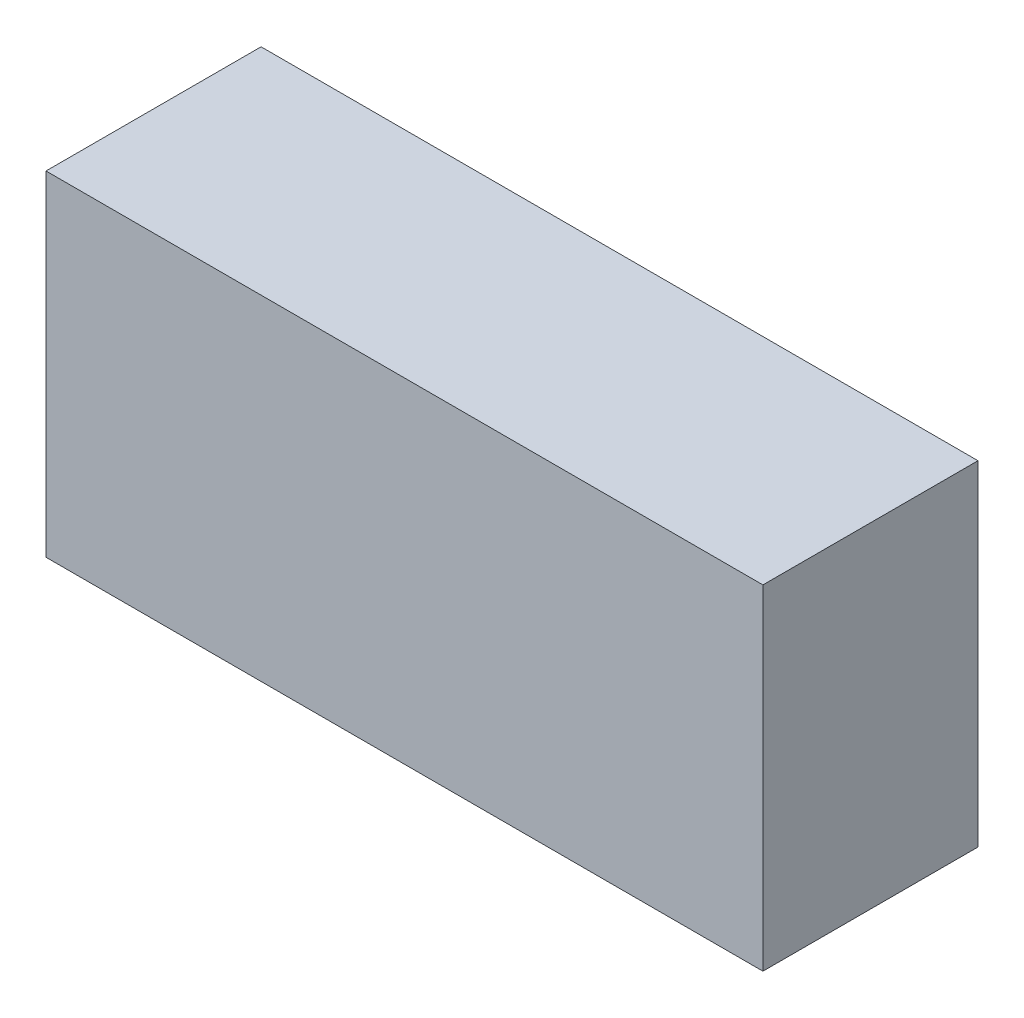
SolidWorks part; units mm, degrees
ref_plane "Спереди" through (0, 0, 0) normal (0, 0, 1) x (1, 0, 0)
ref_plane "Сверху" through (0, 0, 0) normal (0, 1, 0) x (1, 0, 0)
ref_plane "Справа" through (0, 0, 0) normal (1, 0, 0) x (0, 0, -1)
sketch "Эскиз1" plane through (0, 0, 0) normal (0, 0, 1) x (1, 0, 0)
  line L1 (0, 0) -> (150, 0)
  line L2 (0, 0) -> (0, 70)
  line L3 (0, 70) -> (150, 70)
  line L4 (150, 0) -> (150, 70)
  dimension "D1" = 150
  dimension "D2" = 70
extrude "Бобышка-Вытянуть1" add sketch "Эскиз1" along normal blind 45
